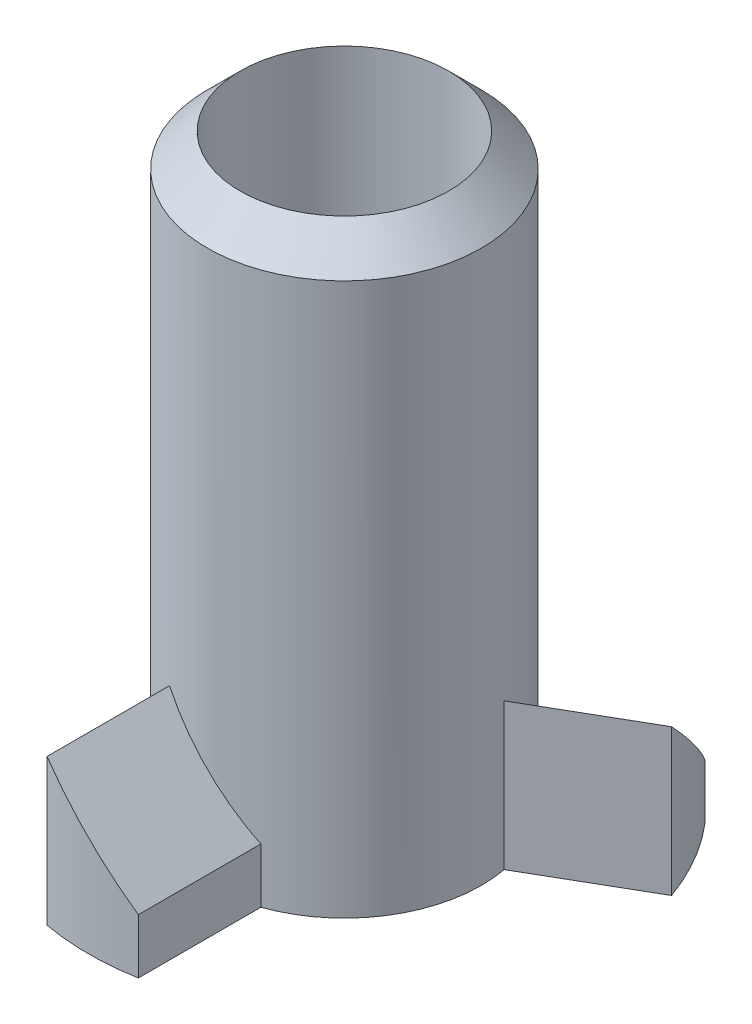
SolidWorks part; units mm, degrees
material "POM"
ref_plane "Ebene vorne" through (0, 0, 0) normal (0, 0, 1) x (1, 0, 0)
ref_plane "Ebene oben" through (0, 0, 0) normal (0, 1, 0) x (1, 0, 0)
ref_plane "Ebene rechts" through (0, 0, 0) normal (1, 0, 0) x (0, 0, -1)
sketch "Skizze1" plane through (0, 0, 0) normal (0, 0, 1) x (1, 0, 0)
  line L0 (0, 0) -> (0, 5.0755) construction
  line L1 (1.425, 0) -> (1.425, 8)
  line L2 (1.425, 8) -> (1.875, 7.55)
  line L3 (1.875, 7.55) -> (1.875, 0)
  line L6 (1.875, 0) -> (1.425, 0)
  dimension "D1" = 2.85
  dimension "D2" = 3.75
  dimension "D3" = 45
  dimension "D4" = 8
revolve "Rotation1" add sketch "Skizze1" angle 360 about L0
sketch "Skizze2" plane through (0, 0, 0) normal (0, 1, 0) x (1, 0, 0)
  line L0 (-0.625, -3.4437) -> (-0.625, -1.7678)
  line L1 (0.625, -3.4437) -> (0.625, -1.7678)
  circle A0 centre (0, 0) radius 1.875 construction
  arc A1 (-0.625, -3.4437) -> (0.625, -3.4437) centre (0, 0) ccw
  arc A2 (-0.625, -1.7678) -> (0.625, -1.7678) centre (0, 0) ccw
  point P4 (0, -3.5)
  dimension "D1" = 3.5
  dimension "D2" = 1.25
extrude "Aufsatz-Linear austragen1" add sketch "Skizze2" along normal blind 2 separate body
sketch "Skizze3" plane through (0, 0, 0) normal (0, 0, 1) x (1, 0, 0)
  line L0 (-0.625, 2) -> (0.625, 0.75)
  line L2 (0.625, 0.75) -> (0.625, 2)
  line L3 (0.625, 2) -> (-0.625, 2)
  dimension "D1" = 45
extrude "Schnitt-Linear austragen1" cut sketch "Skizze3" along normal through all
pattern_circular "Kreismuster1" count 3 over 360 about axis through (0, 0, 0) along (0, 1, 0) of bodies 129
combine bodies "Kombinieren1" operation type add bodies to combine 129 130 131 115
